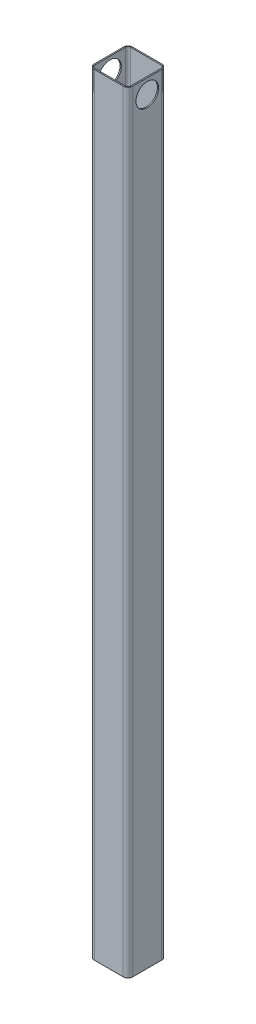
SolidWorks part; units mm, degrees
material "Plain Carbon Steel"
ref_plane "Front Plane" through (0, 0, 0) normal (0, 0, 1) x (1, 0, 0)
ref_plane "Top Plane" through (0, 0, 0) normal (0, 1, 0) x (1, 0, 0)
ref_plane "Right Plane" through (0, 0, 0) normal (1, 0, 0) x (0, 0, -1)
sketch "Sketch1" plane through (0, 0, 0) normal (0, 1, 0) x (1, 0, 0)
  line L0 (-30.9245, -35.687) -> (30.9245, -35.687)
  line L1 (-35.687, -30.9245) -> (-35.687, 30.9245)
  line L2 (30.9245, 35.687) -> (-30.9245, 35.687)
  line L3 (35.687, 30.9245) -> (35.687, -30.9245)
  line L4 (-28.575, -38.1) -> (28.575, -38.1)
  line L5 (-38.1, -28.575) -> (-38.1, 28.575)
  line L6 (28.575, 38.1) -> (-28.575, 38.1)
  line L7 (38.1, 28.575) -> (38.1, -28.575)
  line L10 (0, 35.687) -> (0, -35.687) construction
  arc A0 (38.1, 28.575) -> (28.575, 38.1) centre (28.575, 28.575) ccw
  arc A1 (28.575, -38.1) -> (38.1, -28.575) centre (28.575, -28.575) ccw
  arc A2 (-38.1, -28.575) -> (-28.575, -38.1) centre (-28.575, -28.575) ccw
  arc A3 (-28.575, 38.1) -> (-38.1, 28.575) centre (-28.575, 28.575) ccw
  arc A4 (-30.9245, 35.687) -> (-35.687, 30.9245) centre (-30.9245, 30.9245) ccw
  arc A5 (35.687, 30.9245) -> (30.9245, 35.687) centre (30.9245, 30.9245) ccw
  arc A6 (30.9245, -35.687) -> (35.687, -30.9245) centre (30.9245, -30.9245) ccw
  arc A7 (-35.687, -30.9245) -> (-30.9245, -35.687) centre (-30.9245, -30.9245) ccw
extrude "Boss-Extrude1" add sketch "Sketch1" along normal mid plane 1524
sketch "Sketch2" plane through (38.1, 0, 0) normal (1, 0, 0) x (0, 0, -1)
  line L0 (0, 41.91) -> (0, -41.91) construction
  line L3 (0, 710.692) -> (0, 755.65) construction
  line L4 (-28.575, 762) -> (28.575, 762) construction
  circle A0 centre (0, 733.171) radius 22.479
  dimension "D1" = 44.958
  dimension "D2" = 6.35
extrude "Cut-Extrude1" cut sketch "Sketch2" against normal through all
